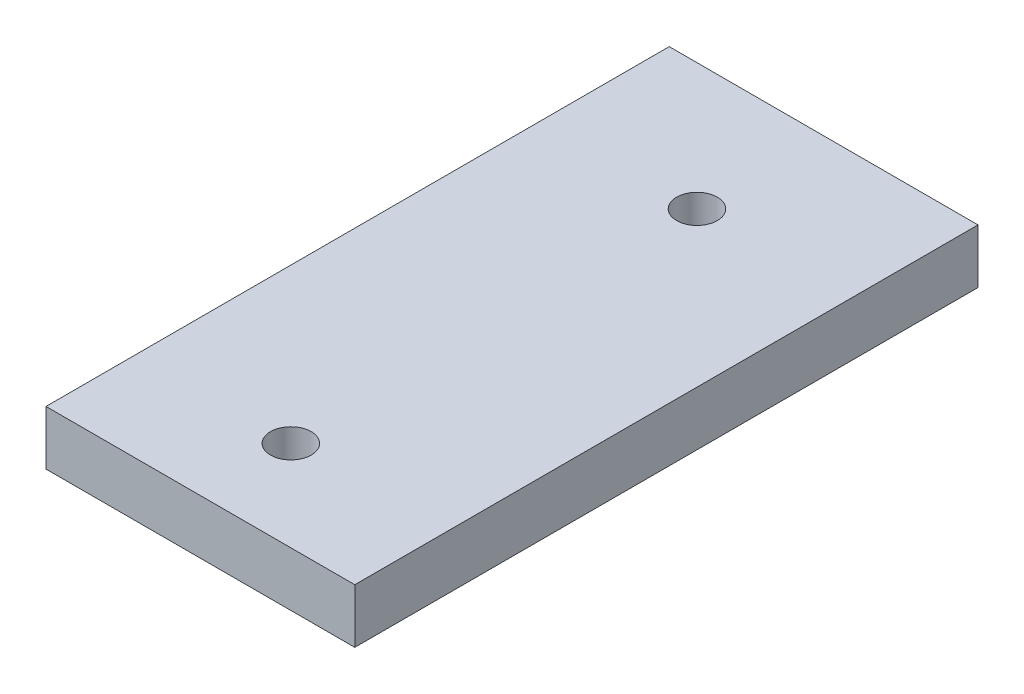
SolidWorks part; units mm, degrees
ref_plane "Front Plane" through (0, 0, 0) normal (0, 0, 1) x (1, 0, 0)
ref_plane "Top Plane" through (0, 0, 0) normal (0, 1, 0) x (1, 0, 0)
ref_plane "Right Plane" through (0, 0, 0) normal (1, 0, 0) x (0, 0, -1)
sketch "Sketch1" plane through (0, 0, 0) normal (0, 1, 0) x (1, 0, 0)
  line L9 (-14.7858, -27.8964) -> (19.3496, -27.8964)
  line L10 (-14.7858, -27.8964) -> (-14.7858, 40.9996)
  line L11 (-14.7858, 40.9996) -> (19.3496, 40.9996)
  line L12 (19.3496, -27.8964) -> (19.3496, 40.9996)
extrude "Boss-Extrude1" add sketch "Sketch1" along normal blind 6
sketch "Sketch2" plane through (0, 6, 0) normal (0, 1, 0) x (1, 0, 0)
  line L0 (19.3496, -17.8964) -> (-14.7858, -17.8964) construction
  line L1 (19.3496, -27.8964) -> (19.3496, 40.9996) construction
  line L2 (-14.7858, 40.9996) -> (-14.7858, -27.8964) construction
  line L3 (-14.7858, -27.8964) -> (19.3496, -27.8964) construction
  line L4 (-14.7858, 26.9996) -> (19.3496, 26.9996) construction
  line L5 (19.3496, 40.9996) -> (-14.7858, 40.9996) construction
  line L6 (2.2819, 40.9996) -> (2.2819, -27.8964) construction
  circle A0 centre (2.2819, -17.8964) radius 2.25
  circle A1 centre (2.2819, 26.9996) radius 2.25
  dimension "D3" = 4.5
  dimension "D4" = 4.5
  dimension "D1" = 10
  dimension "D2" = 14
extrude "Cut-Extrude1" cut sketch "Sketch2" against normal up to next
